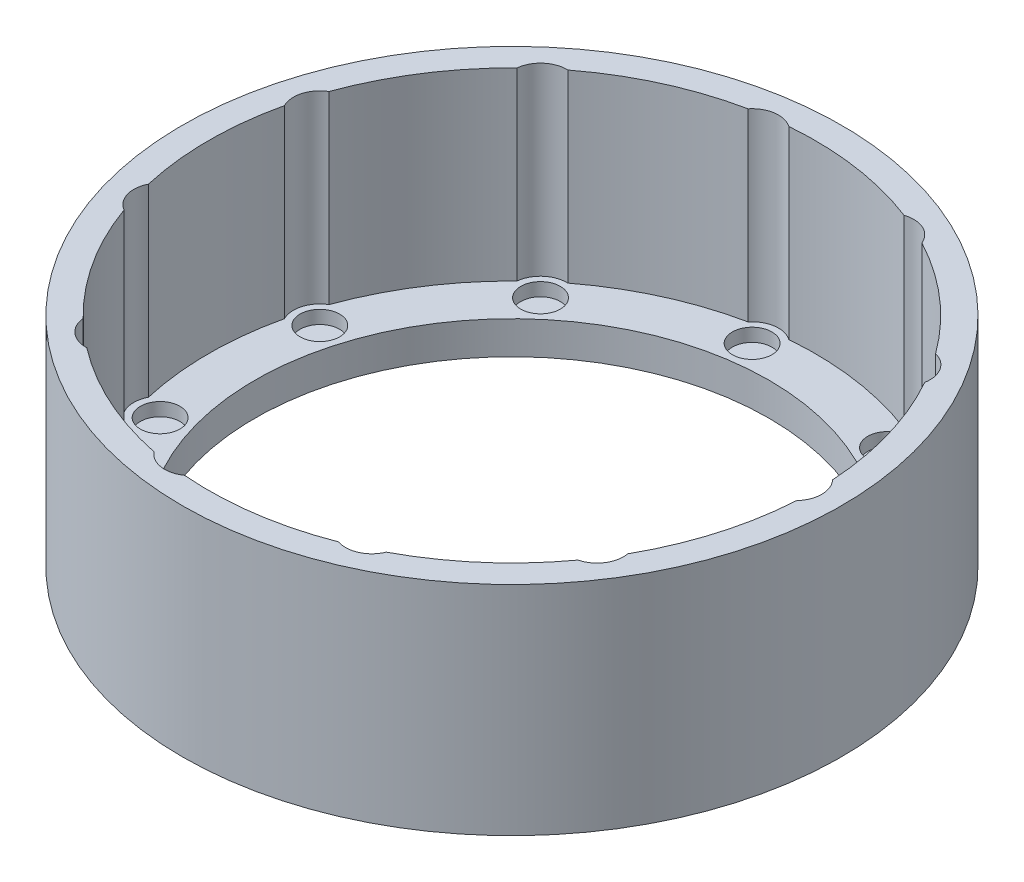
SolidWorks part; units mm, degrees
material "PET"
ref_plane "Front Plane" through (0, 0, 0) normal (0, 0, 1) x (1, 0, 0)
ref_plane "Top Plane" through (0, 0, 0) normal (0, 1, 0) x (1, 0, 0)
ref_plane "Right Plane" through (0, 0, 0) normal (1, 0, 0) x (0, 0, -1)
sketch "Sketch1" plane through (0, 0, 0) normal (0, 1, 0) x (1, 0, 0)
  line L0 (0, 0) -> (50, 0) construction
  circle A0 centre (0, 0) radius 50
  dimension "D1" = 100
extrude "Boss-Extrude1" add sketch "Sketch1" along normal blind 5
sketch "Sketch2" plane through (0, 5, 0) normal (0, 1, 0) x (1, 0, 0)
  line L0 (0, 0) -> (50, 0) construction
  circle A0 centre (0, 0) radius 50 construction
  circle A1 centre (43, 0) radius 2.5
  circle A2 centre (36.1739, -23.2476) radius 2.5
  circle A3 centre (17.8628, -39.1142) radius 2.5
  circle A4 centre (-6.1195, -42.5623) radius 2.5
  circle A5 centre (-28.159, -32.4972) radius 2.5
  circle A6 centre (-41.2582, -12.1145) radius 2.5
  circle A7 centre (-41.2582, 12.1145) radius 2.5
  circle A8 centre (-28.159, 32.4972) radius 2.5
  circle A9 centre (-6.1195, 42.5623) radius 2.5
  circle A10 centre (17.8628, 39.1142) radius 2.5
  circle A11 centre (36.1739, 23.2476) radius 2.5
  point P30 (0, 0)
  dimension "D1" = 5
  dimension "D2" = 43
  dimension "D3" = 11
extrude "Boss-Extrude2" add sketch "Sketch2" along normal blind 30
sketch "Sketch3" plane through (0, 5, 0) normal (0, 1, 0) x (1, 0, 0)
  arc A0 (45.9186, -2.7353) -> (45.9186, 2.7353) centre (43, 0) ccw
  arc A23 (37.1504, -27.1265) -> (40.108, -22.5244) centre (36.1739, -23.2476) ccw
  arc A24 (16.5872, -42.9053) -> (21.5634, -40.6328) centre (17.8628, -39.1142) ccw
  arc A25 (-9.2423, -45.0619) -> (-3.8275, -45.8405) centre (-6.1195, -42.5623) ccw
  arc A26 (-32.1375, -32.9117) -> (-28.0031, -36.4942) centre (-28.159, -32.4972) ccw
  arc A27 (-44.8292, -10.3123) -> (-43.288, -15.5612) centre (-41.2582, -12.1145) ccw
  arc A28 (-43.288, 15.5612) -> (-44.8292, 10.3123) centre (-41.2582, 12.1145) ccw
  arc A29 (-28.0031, 36.4942) -> (-32.1375, 32.9117) centre (-28.159, 32.4972) ccw
  arc A30 (-3.8275, 45.8405) -> (-9.2423, 45.0619) centre (-6.1195, 42.5623) ccw
  arc A31 (21.5634, 40.6328) -> (16.5872, 42.9053) centre (17.8628, 39.1142) ccw
  arc A32 (40.108, 22.5244) -> (37.1504, 27.1265) centre (36.1739, 23.2476) ccw
  circle A33 centre (0, 0) radius 50
  arc A34 (-32.1375, 32.9117) -> (-43.288, 15.5612) centre (0, 0) ccw
  arc A35 (-9.2423, 45.0619) -> (-28.0031, 36.4942) centre (0, 0) ccw
  arc A36 (16.5872, 42.9053) -> (-3.8275, 45.8405) centre (0, 0) ccw
  arc A37 (37.1504, 27.1265) -> (21.5634, 40.6328) centre (0, 0) ccw
  arc A38 (45.9186, 2.7353) -> (40.108, 22.5244) centre (0, 0) ccw
  arc A39 (40.108, -22.5244) -> (45.9186, -2.7353) centre (0, 0) ccw
  arc A40 (21.5634, -40.6328) -> (37.1504, -27.1265) centre (0, 0) ccw
  arc A41 (-3.8275, -45.8405) -> (16.5872, -42.9053) centre (0, 0) ccw
  arc A42 (-28.0031, -36.4942) -> (-9.2423, -45.0619) centre (0, 0) ccw
  arc A43 (-43.288, -15.5612) -> (-32.1375, -32.9117) centre (0, 0) ccw
  arc A44 (-44.8292, 10.3123) -> (-44.8292, -10.3123) centre (0, 0) ccw
  point P38 (0, 0)
  dimension "D1" = 92
  dimension "D3" = 11
  dimension "D2" = 100
  dimension "D4" = 4
extrude "Boss-Extrude3" add sketch "Sketch3" along normal blind 28
sketch "Sketch4" plane through (0, 5, 0) normal (0, 1, 0) x (1, 0, 0)
  circle A0 centre (0, 0) radius 39
  dimension "D1" = 78
extrude "Cut-Extrude1" cut sketch "Sketch4" against normal blind 6
sketch "Sketch5" plane through (0, 5, 0) normal (0, 1, 0) x (1, 0, 0)
  circle A0 centre (43, 0) radius 3
  circle A1 centre (36.1739, -23.2476) radius 3
  circle A2 centre (17.8628, -39.1142) radius 3
  circle A3 centre (-6.1195, -42.5623) radius 3
  circle A4 centre (-28.159, -32.4972) radius 3
  circle A5 centre (-41.2582, -12.1145) radius 3
  circle A6 centre (-41.2582, 12.1145) radius 3
  circle A7 centre (-28.159, 32.4972) radius 3
  circle A8 centre (-6.1195, 42.5623) radius 3
  circle A9 centre (17.8628, 39.1142) radius 3
  circle A10 centre (36.1739, 23.2476) radius 3
  point P26 (0, 0)
  dimension "D2" = 6
  dimension "D1" = 11
extrude "Cut-Extrude2" cut sketch "Sketch5" along normal mid plane 88
sketch "Sketch6" plane through (0, 0, 0) normal (0, -1, 0) x (1, 0, 0)
  circle A0 centre (0, 0) radius 39
  circle A1 centre (0, 0) radius 50
extrude "Boss-Extrude4" add sketch "Sketch6" against normal blind 3
